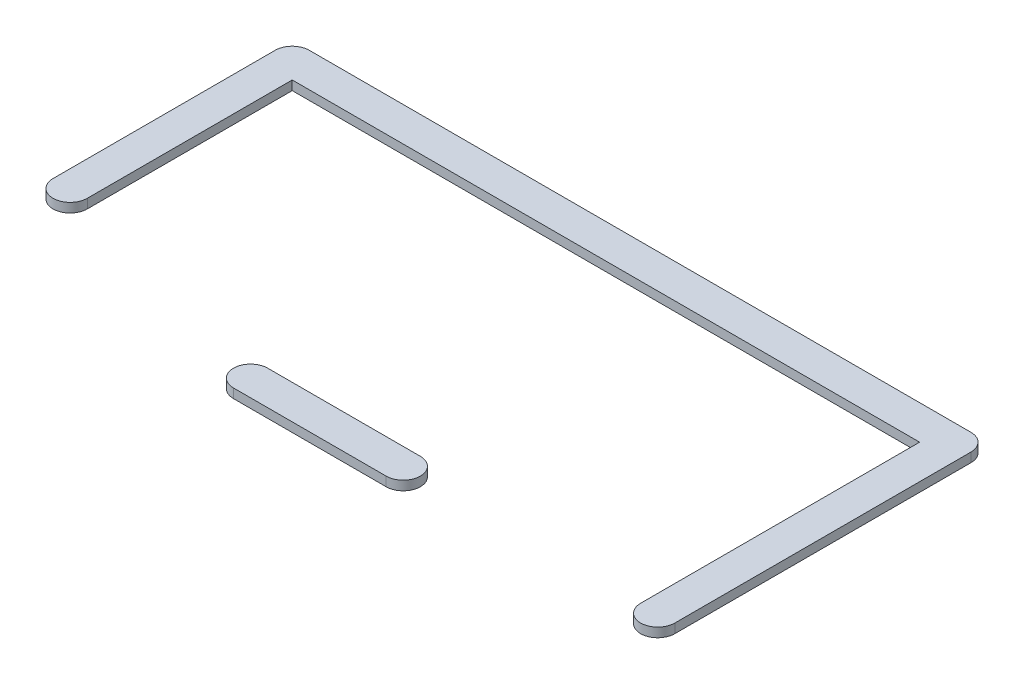
SolidWorks part; units mm, degrees
ref_plane "前视基准面" through (0, 0, 0) normal (0, 0, 1) x (1, 0, 0)
ref_plane "上视基准面" through (0, 0, 0) normal (0, 1, 0) x (1, 0, 0)
ref_plane "右视基准面" through (0, 0, 0) normal (1, 0, 0) x (0, 0, -1)
sketch "草图5" plane through (0, 0, 0) normal (0, 1, 0) x (1, 0, 0)
  line L0 (0, 0) -> (1430, 0) construction
  line L1 (1430, 0) -> (1430, -640) construction
  line L2 (0, -480) -> (0, 0) construction
  line L3 (550, -640) -> (880, -640) construction
  line L4 (37, -480) -> (37, -37)
  line L5 (37, -37) -> (1393, -37)
  line L6 (1393, -37) -> (1393, -640)
  line L7 (-37, -480) -> (-37, 0)
  line L8 (0, 37) -> (1430, 37)
  line L9 (1467, 0) -> (1467, -640)
  line L10 (550, -677) -> (880, -677)
  line L11 (550, -603) -> (880, -603)
  line L12 (-37, 37) -> (1467, 37) construction
  line L13 (-37, -480) -> (-37, 37) construction
  line L14 (1467, 37) -> (1467, -640) construction
  circle A0 centre (550, -640) radius 37 construction
  circle A1 centre (880, -640) radius 37 construction
  circle A2 centre (1430, -640) radius 37 construction
  circle A3 centre (1430, 0) radius 37 construction
  circle A4 centre (0, -480) radius 37 construction
  circle A5 centre (0, 0) radius 37 construction
  circle A6 centre (550, -640) radius 37 construction
  circle A7 centre (880, -640) radius 37 construction
  circle A8 centre (1430, -640) radius 37 construction
  arc A9 (1467, 0) -> (1430, 37) centre (1430, 0) ccw
  circle A10 centre (0, -480) radius 37 construction
  arc A11 (0, 37) -> (-37, 0) centre (0, 0) ccw
  arc A12 (-37, -480) -> (37, -480) centre (0, -480) ccw
  arc A13 (1393, -640) -> (1467, -640) centre (1430, -640) ccw
  arc A14 (880, -603) -> (880, -677) centre (880, -640) cw
  arc A15 (550, -603) -> (550, -677) centre (550, -640) ccw
  dimension "D1" = 37
  dimension "D2" = 37
  dimension "D3" = 37
  dimension "D4" = 37
extrude "凸台-拉伸3" add sketch "草图5" against normal blind 20
